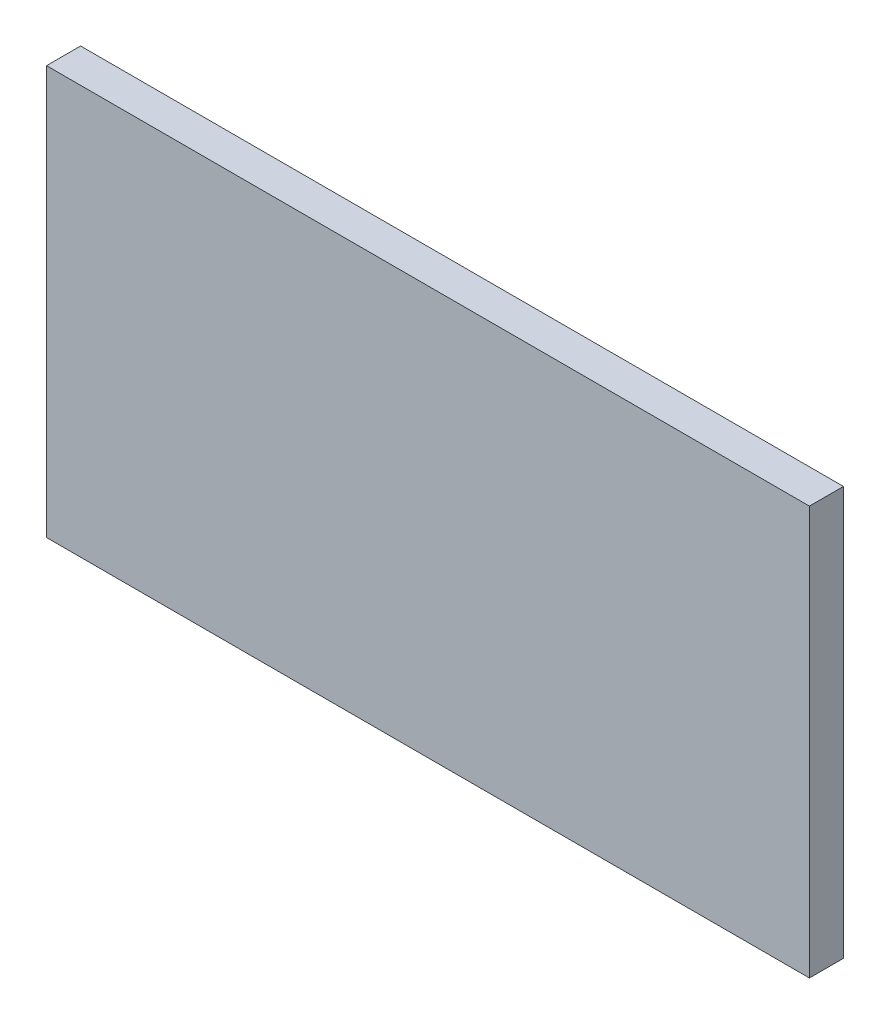
SolidWorks part; units mm, degrees
material "6063-T6"
ref_plane "Front" through (0, 0, 0) normal (0, 0, 1) x (1, 0, 0)
ref_plane "Top" through (0, 0, 0) normal (0, 1, 0) x (1, 0, 0)
ref_plane "Right" through (0, 0, 0) normal (1, 0, 0) x (0, 0, -1)
sketch "Sketch1" plane through (0, 0, 0) normal (0, 0, 1) x (1, 0, 0)
  line L1 (0, 0) -> (71.12, 0)
  line L2 (0, 0) -> (0, 38.1)
  line L3 (0, 38.1) -> (71.12, 38.1)
  line L4 (71.12, 0) -> (71.12, 38.1)
  line L5 (0, 0) -> (71.12, 38.1) construction
  line L6 (0, 38.1) -> (71.12, 0) construction
  point P4 (35.56, 19.05)
  dimension "D1" = 38.1
  dimension "D2" = 71.12
extrude "Boss-Extrude1" add sketch "Sketch1" along normal blind 3.175
